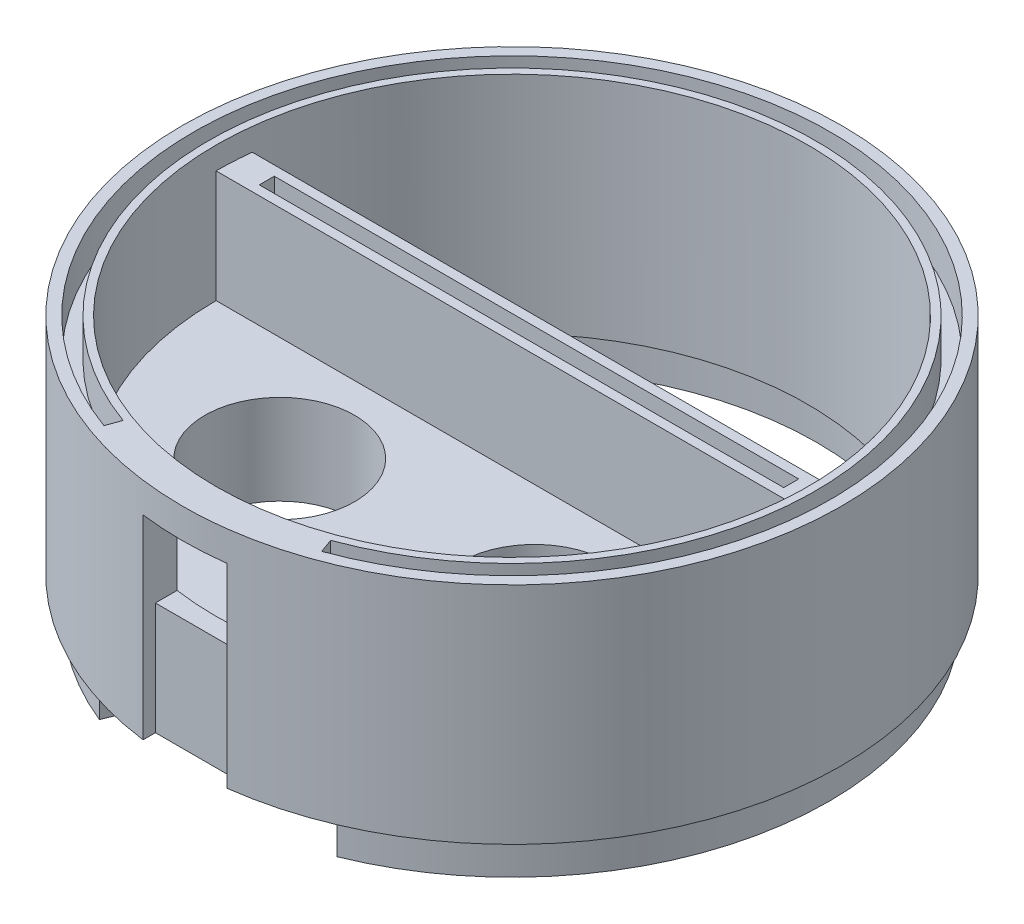
SolidWorks part; units mm, degrees
other "Markup1"
sketch "Sketch36" plane through (-70, 25, 70) normal (-0.3758, -0.347, 0.8593) x (0.9047, -0.338, 0.2592)
ref_plane "Front Plane" through (0, 0, 0) normal (0, 0, 1) x (1, 0, 0)
ref_plane "Top Plane" through (0, 0, 0) normal (0, 1, 0) x (1, 0, 0)
ref_plane "Right Plane" through (0, 0, 0) normal (1, 0, 0) x (0, 0, -1)
sketch "Sketch1" plane through (0, 0, 0) normal (0, 1, 0) x (1, 0, 0)
  circle A0 centre (0, 0) radius 44
  dimension "D1" = 88
extrude "Boss-Extrude1" add sketch "Sketch1" along normal blind 180
ref_plane "Plane4" through (0, 25, 0) normal (0, 1, 0) x (1, 0, 0)
sketch "Sketch2" plane through (0, 25, 0) normal (0, 1, 0) x (1, 0, 0)
  circle A0 centre (0, 0) radius 70
ref_plane "Plane5" through (0, 5, 0) normal (0, 1, 0) x (1, 0, 0)
ref_plane "Plane6" through (0, 100, 0) normal (0, 1, 0) x (1, 0, 0)
ref_plane "Plane7" through (0, 0, 42) normal (0, 0, 1) x (1, 0, 0)
sketch "Sketch7" plane through (0, 25, 0) normal (0, 1, 0) x (1, 0, 0)
  circle A0 centre (0, 0) radius 39.5
  dimension "D1" = 79
extrude "Cut-Extrude1" cut sketch "Sketch7" along normal blind 115
ref_plane "Plane8" through (0, 41, 0) normal (0, 1, 0) x (1, 0, 0)
sketch "Sketch8" plane through (0, 41, 0) normal (0, 1, 0) x (1, 0, 0)
  circle A0 centre (0, 0) radius 35
extrude "Cut-Extrude2" cut sketch "Sketch8" against normal blind 18
sketch "Sketch9" plane through (0, 180, 0) normal (0, 1, 0) x (1, 0, 0)
  line L0 (0, 0) -> (44, 0) construction
  line L1 (0, 0) -> (0, 40.5327) construction
  circle A0 centre (29, 10) radius 6
  circle A1 centre (0, 0) radius 44 construction
  dimension "D1" = 10
  dimension "D2" = 12
  dimension "D3" = 15
ref_plane "Plane9" through (0, 174, 0) normal (0, 1, 0) x (1, 0, 0)
ref_plane "Plane10" through (0, 156, 0) normal (0, 1, 0) x (1, 0, 0)
sketch "Sketch12" plane through (0, 0, 42) normal (0, 0, 1) x (1, 0, 0)
  line L0 (0, 167) -> (0, 10.2975) construction
  line L1 (0, -77) -> (0, 77) construction
  line L2 (-5.6, 10.2975) -> (5.6, 10.2975)
  line L3 (-5.6, 10.2975) -> (-5.6, 167)
  line L4 (-5.6, 167) -> (5.6, 167)
  line L5 (5.6, 10.2975) -> (5.6, 167)
  line L6 (44, 180) -> (-44, 180) construction
  point P0 (0, 10.2975)
  point P1 (0, 167)
  dimension "D1" = 11.2
  dimension "D2" = 13
extrude "Cut-Extrude5" cut sketch "Sketch12" along normal blind 13.6
sketch "Sketch14" plane through (0, 0, 42) normal (0, 0, 1) x (1, 0, 0)
  line L0 (-5.6, 167) -> (-5.6, 10.2975) construction
  line L1 (-5.6, 18.9739) -> (5.6, 18.9739)
  line L2 (-5.6, 18.9739) -> (-5.6, 10.2975)
  line L3 (-5.6, 10.2975) -> (5.6, 10.2975)
  line L4 (5.6, 18.9739) -> (5.6, 10.2975)
extrude "Cut-Extrude6" cut sketch "Sketch14" against normal blind 18
sketch "Sketch18" plane through (0, 180, 0) normal (0, 1, 0) x (1, 0, 0)
  circle A1 centre (0, 0) radius 39.5
  dimension "D1" = 79
extrude "Cut-Extrude8" cut sketch "Sketch18" against normal blind 12
sketch "Sketch10" plane through (0, 174, 0) normal (0, 1, 0) x (1, 0, 0)
  line L0 (-39.5, 0) -> (39.5, 0)
  line L3 (-77, 0) -> (77, 0) construction
  arc A0 (-39.5, 0) -> (39.5, 0) centre (0, 0) ccw
  point P6 (0, 0)
  dimension "D1" = 39.5
extrude "Cut-Extrude4" cut sketch "Sketch10" against normal mid plane 42
sketch "Sketch20" plane through (0, 168, 0) normal (0, 1, 0) x (1, 0, 0)
  line L0 (39.5, 0) -> (-39.5, 0) construction
  line L1 (9, 26) -> (-15, 26)
  line L2 (14, 21) -> (14, 10)
  line L3 (9, 5) -> (-15, 5)
  line L4 (-20, 21) -> (-20, 10)
  line L5 (0, 0) -> (0, 44) construction
  circle A2 centre (0, 0) radius 44 construction
  arc A3 (9, 26) -> (14, 21) centre (9, 21) cw
  arc A4 (-20, 10) -> (-15, 5) centre (-15, 10) ccw
  arc A5 (-20, 21) -> (-15, 26) centre (-15, 21) cw
  arc A6 (9, 5) -> (14, 10) centre (9, 10) ccw
  dimension "D2" = 26
  dimension "D5" = 5
  dimension "D6" = 5
  dimension "D1" = 5
  dimension "D3" = 14
  dimension "D4" = 20
extrude "Cut-Extrude9" cut sketch "Sketch20" against normal blind 28
sketch "Sketch21" plane through (0, 5, 0) normal (0, 1, 0) x (1, 0, 0)
  circle A0 centre (0, 0) radius 44
  circle A1 centre (0, 0) radius 44 construction
extrude "Cut-Extrude10" cut sketch "Sketch21" against normal blind 10
sketch "Sketch22" plane through (0, 168, 0) normal (0, 1, 0) x (1, 0, 0)
  line L0 (0, 0) -> (0, 44) construction
  line L1 (39.5, 0) -> (-39.5, 0) construction
  line L2 (-15, 5) -> (9, 5) construction
  line L3 (-36.447, 5) -> (36.6796, 5)
  circle A0 centre (0, 0) radius 44 construction
  point P7 (0, 5)
sketch "Sketch23" plane through (0, 168, 0) normal (0, 1, 0) x (1, 0, 0)
  line L0 (39.5, 0) -> (-39.5, 0) construction
  line L1 (-34.7006, 4.5684) -> (34.7006, 4.5684)
  arc A0 (34.7006, 4.5684) -> (-34.7006, 4.5684) centre (0, 0) ccw
extrude "Cut-Extrude11" cut sketch "Sketch23" against normal blind 50
sketch "Sketch24" plane through (0, 153, 0) normal (0, 1, 0) x (1, 0, 0)
  line L0 (0, 0) -> (0, -39.5) construction
  line L1 (39.5, 0) -> (-39.5, 0) construction
  arc A0 (-39.5, 0) -> (39.5, 0) centre (0, 0) ccw construction
  circle A1 centre (-17, -14) radius 10
  circle A2 centre (17, -14) radius 10
  dimension "D1" = 34
  dimension "D2" = 20
  dimension "D3" = 14
extrude "Cut-Extrude12" cut sketch "Sketch24" against normal blind 16
ref_plane "Plane11" through (0, 0, 39.5) normal (0, 0, -1) x (-1, 0, 0)
sketch "Sketch16" plane through (0, 0, 39.5) normal (0, 0, 1) x (1, 0, 0)
  line L0 (5.6, 18.9739) -> (5.6, 167) construction
  line L1 (-5.6, 167) -> (5.6, 167)
  line L2 (-5.6, 167) -> (-5.6, 163.0537)
  line L3 (-5.6, 163.0537) -> (5.6, 163.0537)
  line L4 (5.6, 167) -> (5.6, 163.0537)
extrude "Cut-Extrude7" [suppressed] cut sketch "Sketch16" against normal blind 18
sketch "Sketch26" plane through (0, 0, 42) normal (0, 0, 1) x (1, 0, 0)
  line L0 (-5.6, 167) -> (5.6, 167) construction
  line L1 (-5.6, 167) -> (5.6, 167)
  line L2 (-5.6, 167) -> (-5.6, 156)
  line L3 (-5.6, 156) -> (5.6, 156)
  line L4 (5.6, 167) -> (5.6, 156)
  line L5 (-5.6, 167) -> (-5.6, 10.2975) construction
  line L6 (5.6, 18.9739) -> (5.6, 167) construction
  dimension "D1" = 11
extrude "Cut-Extrude13" cut sketch "Sketch26" against normal blind 14
sketch "Sketch27" plane through (0, 5, 0) normal (0, -1, 0) x (1, 0, 0)
  circle A0 centre (0, 0) radius 39
  circle A1 centre (0, 0) radius 44 construction
  dimension "D1" = 5
extrude "Cut-Extrude14" cut sketch "Sketch27" against normal blind 30
sketch "Sketch28" plane through (0, 5, 0) normal (0, -1, 0) x (1, 0, 0)
  circle A0 centre (0, 0) radius 42
  circle A1 centre (0, 0) radius 47
  dimension "D1" = 84
  dimension "D2" = 94
extrude "Boss-Extrude2" add sketch "Sketch28" along normal blind 20
sketch "Sketch29" plane through (0, 168, 0) normal (0, 1, 0) x (1, 0, 0)
  line L0 (-39.2349, 4.5684) -> (-34.7006, 4.5684)
  line L1 (-34.7006, 4.5684) -> (34.7006, 4.5684) construction
  line L2 (39.5, 0) -> (-39.5, 0) construction
  line L3 (34.7006, 4.5684) -> (39.2349, 4.5684)
  circle A0 centre (0, 0) radius 39.5 construction
  arc A1 (39.2349, 4.5684) -> (-39.2349, 4.5684) centre (0, 0) ccw
  arc A2 (34.7006, 4.5684) -> (-34.7006, 4.5684) centre (0, 0) ccw
  point P14 (34.7006, 4.5684)
extrude "Cut-Extrude15" cut sketch "Sketch29" against normal blind 40
sketch "Sketch30" plane through (0, -15, 0) normal (0, -1, 0) x (1, 0, 0)
  circle A0 centre (0, 0) radius 47
  circle A1 centre (0, 0) radius 47 construction
extrude "Cut-Extrude16" cut sketch "Sketch30" against normal blind 20
sketch "Sketch31" plane through (0, 5, 0) normal (0, -1, 0) x (1, 0, 0)
  circle A0 centre (0, 0) radius 42
  dimension "D1" = 84
extrude "Boss-Extrude3" [suppressed] add sketch "Sketch31" against normal blind 5
ref_plane "Plane12" through (0, 141, 0) normal (0, 1, 0) x (1, 0, 0)
sketch "Sketch33" plane through (0, 141, 0) normal (0, 1, 0) x (1, 0, 0)
  circle A0 centre (0, 0) radius 44
extrude "Cut-Extrude17" cut sketch "Sketch33" against normal through all
sketch "Sketch34" plane through (0, 141, 0) normal (0, -1, 0) x (1, 0, 0)
  line L0 (0, 0) -> (18.9772, 46.9703) construction
  line L1 (0, 0) -> (0, 56.5295) construction
  line L2 (5.6, 43.6422) -> (5.6, 42) construction
  line L3 (-5.6, 42) -> (-5.6, 43.6422) construction
  line L4 (15.2465, 37.7364) -> (15.8459, 39.2199)
  line L5 (-15.2465, 37.7364) -> (-15.8459, 39.2199)
  arc A0 (-15.8459, 39.2199) -> (15.8459, 39.2199) centre (0, 0) ccw
  arc A1 (-15.2465, 37.7364) -> (15.2465, 37.7364) centre (0, 0) ccw
  dimension "D1" = 84.6
  dimension "D2" = 81.4
  dimension "D3" = 22
extrude "Boss-Extrude4" add sketch "Sketch34" along normal blind 5
sketch "Sketch35" plane through (0, 168, 0) normal (0, 1, 0) x (1, 0, 0)
  line L1 (35, 1.2684) -> (-35, 1.2684)
  line L2 (35, 1.2684) -> (35, 3.2684)
  line L3 (35, 3.2684) -> (-35, 3.2684)
  line L4 (-35, 1.2684) -> (-35, 3.2684)
  line L5 (0, 0) -> (0, 4.5684) construction
  line L6 (39.5, 0) -> (-39.5, 0) construction
  line L7 (-39.2349, 4.5684) -> (39.2349, 4.5684) construction
  dimension "D1" = 70
  dimension "D2" = 1.3
  dimension "D3" = 2
extrude "Cut-Extrude18" cut sketch "Sketch35" against normal blind 5
sketch "Sketch37" plane through (0, 180, 0) normal (0, 1, 0) x (1, 0, 0)
  circle A0 centre (0, 0) radius 44
extrude "Cut-Extrude19" cut sketch "Sketch37" against normal blind 9
sketch "Sketch38" plane through (0, 171, 0) normal (0, 1, 0) x (1, 0, 0)
  line L0 (-14.5359, -39.9369) -> (-13.8518, -38.0576)
  line L1 (0, 0) -> (-14.5359, -39.9369) construction
  line L2 (0, 0) -> (0, -42.5) construction
  line L3 (0, 0) -> (0, -42.5) construction
  line L4 (-5.6, -42) -> (-5.6, -43.6422) construction
  line L5 (14.5359, -39.9369) -> (13.8518, -38.0576)
  line L6 (5.6, -43.6422) -> (5.6, -42) construction
  arc A0 (14.5359, -39.9369) -> (-14.5359, -39.9369) centre (0, 0) ccw
  arc A1 (13.8518, -38.0576) -> (-13.8518, -38.0576) centre (0, 0) ccw
  point P4 (-13.8518, -38.0576)
  dimension "D1" = 81
  dimension "D2" = 85
  dimension "D3" = 20
extrude "Cut-Extrude20" cut sketch "Sketch38" against normal blind 5
